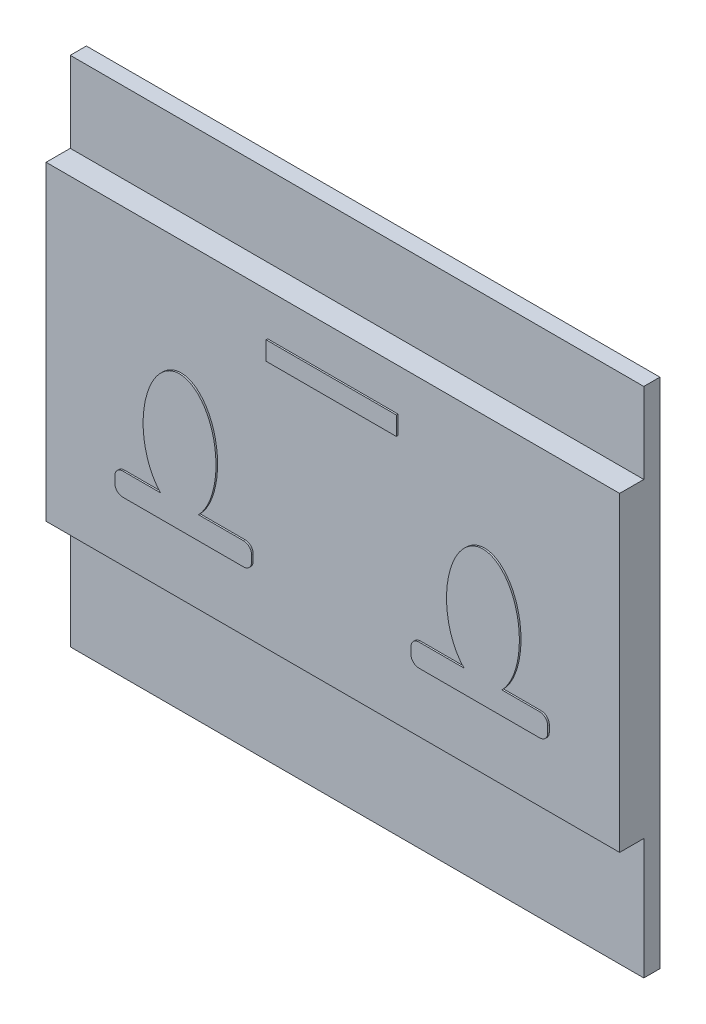
SolidWorks part; units mm, degrees
ref_plane "前视基准面" through (0, 0, 0) normal (0, 0, 1) x (1, 0, 0)
ref_plane "上视基准面" through (0, 0, 0) normal (0, 1, 0) x (1, 0, 0)
ref_plane "右视基准面" through (0, 0, 0) normal (1, 0, 0) x (0, 0, -1)
sketch "草图1" plane through (0, 0, 0) normal (0, 0, 1) x (1, 0, 0)
  line L1 (17.8, 15.9) -> (-17.8, 15.9)
  line L2 (17.8, 15.9) -> (17.8, -15.9)
  line L3 (17.8, -15.9) -> (-17.8, -15.9)
  line L4 (-17.8, 15.9) -> (-17.8, -15.9)
  line L5 (17.8, 15.9) -> (-17.8, -15.9) construction
  line L6 (17.8, -15.9) -> (-17.8, 15.9) construction
  point P0 (0, 0)
  dimension "D1" = 35.6
  dimension "D2" = 31.8
extrude "凸台-拉伸1" add sketch "草图1" along normal blind 1
sketch "草图2" plane through (0, 0, 1) normal (0, 0, 1) x (1, 0, 0)
  line L0 (17.8, -15.9) -> (17.8, 15.9) construction
  line L1 (-17.8, 10.9) -> (17.8, 10.9)
  line L2 (-17.8, 10.9) -> (-17.8, -8.4)
  line L3 (-17.8, -8.4) -> (17.8, -8.4)
  line L4 (17.8, 10.9) -> (17.8, -8.4)
  line L5 (-17.8, 10.9) -> (17.8, -8.4) construction
  line L6 (-17.8, -8.4) -> (17.8, 10.9) construction
  line L7 (17.8, 15.9) -> (-17.8, 15.9) construction
  line L8 (-17.8, -15.9) -> (17.8, -15.9) construction
  point P0 (0, 1.25)
  dimension "D1" = 5
  dimension "D2" = 7.5
extrude "凸台-拉伸2" add sketch "草图2" along normal blind 1.5
sketch "草图3" plane through (0, 0, 2.5) normal (0, 0, 1) x (1, 0, 0)
  line L0 (0, -8.4) -> (0, 10.9) construction
  line L1 (-17.8, -8.4) -> (17.8, -8.4) construction
  line L2 (17.8, 10.9) -> (-17.8, 10.9) construction
  line L3 (8.2379, -3.2167) -> (5.4455, -3.2167)
  line L4 (12.9346, -4.6232) -> (5.4455, -4.6232)
  line L5 (13.4346, -4.1232) -> (13.4346, -3.7167)
  line L6 (12.9346, -3.2167) -> (10.5943, -3.2167)
  line L7 (4.9455, -4.1232) -> (4.9455, -3.7167)
  line L8 (-4.0414, 8.2862) -> (4.0414, 8.2862)
  line L9 (-4.0414, 8.2862) -> (-4.0414, 7.1309)
  line L10 (-4.0414, 7.1309) -> (4.0414, 7.1309)
  line L11 (4.0414, 8.2862) -> (4.0414, 7.1309)
  line L12 (-4.9455, -4.1232) -> (-4.9455, -3.7167)
  line L13 (-12.9346, -3.2167) -> (-10.5943, -3.2167)
  line L14 (-13.4346, -4.1232) -> (-13.4346, -3.7167)
  line L15 (-12.9346, -4.6232) -> (-5.4455, -4.6232)
  line L16 (-8.2379, -3.2167) -> (-5.4455, -3.2167)
  arc A0 (4.9455, -4.1232) -> (5.4455, -4.6232) centre (5.4455, -4.1232) ccw
  arc A1 (4.9455, -3.7167) -> (5.4455, -3.2167) centre (5.4455, -3.7167) cw
  arc A2 (12.9346, -3.2167) -> (13.4346, -3.7167) centre (12.9346, -3.7167) cw
  arc A3 (13.4346, -4.1232) -> (12.9346, -4.6232) centre (12.9346, -4.1232) cw
  arc A4 (-13.4346, -4.1232) -> (-12.9346, -4.6232) centre (-12.9346, -4.1232) ccw
  arc A5 (-12.9346, -3.2167) -> (-13.4346, -3.7167) centre (-12.9346, -3.7167) ccw
  arc A6 (-4.9455, -3.7167) -> (-5.4455, -3.2167) centre (-5.4455, -3.7167) ccw
  arc A7 (-4.9455, -4.1232) -> (-5.4455, -4.6232) centre (-5.4455, -4.1232) cw
  ellipse E0 centre (9.4161, 0) end of major axis (9.4161, -3.7692) minor radius 2.2604 (10.5943, -3.2167) -> (8.2379, -3.2167) ccw
  ellipse E1 centre (-9.4161, 0) end of major axis (-9.4161, -3.7692) minor radius 2.2604 (-10.5943, -3.2167) -> (-8.2379, -3.2167) cw
  point P18 (0, 8.2862)
  point P50 (0, 7.1309)
  dimension "D1" = 0.5
extrude "凸台-拉伸3" add sketch "草图3" along normal blind 0.1
